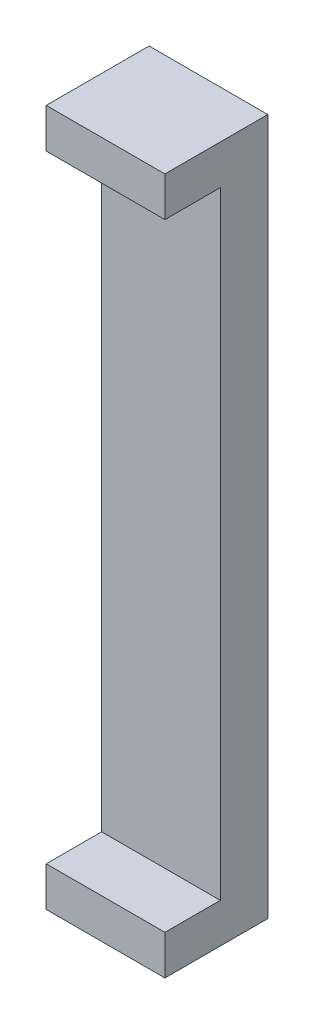
SolidWorks part; units mm, degrees
ref_plane "Front Plane" through (0, 0, 0) normal (0, 0, 1) x (1, 0, 0)
ref_plane "Top Plane" through (0, 0, 0) normal (0, 1, 0) x (1, 0, 0)
ref_plane "Right Plane" through (0, 0, 0) normal (1, 0, 0) x (0, 0, -1)
sketch "Sketch1" plane through (0, 0, 0) normal (0, 0, 1) x (1, 0, 0)
  line L1 (-7.5, 0) -> (7.5, 0)
  line L2 (-7.5, 0) -> (-7.5, 88)
  line L3 (-7.5, 88) -> (7.5, 88)
  line L4 (7.5, 0) -> (7.5, 88)
  point P4 (0, 0)
  dimension "D1" = 15
  dimension "D2" = 88
extrude "Boss-Extrude1" add sketch "Sketch1" along normal mid plane 6
sketch "Sketch2" plane through (0, 0, 0) normal (0, 0, 1) x (1, 0, 0)
  line L0 (7.5, 0) -> (7.5, 88) construction
  line L1 (-7.5, 0) -> (7.5, 0)
  line L2 (-7.5, 0) -> (-7.5, 5)
  line L3 (-7.5, 5) -> (7.5, 5)
  line L4 (7.5, 0) -> (7.5, 5)
  dimension "D1" = 5
extrude "Boss-Extrude2" add sketch "Sketch2" along normal blind 10
sketch "Sketch3" plane through (0, 0, 0) normal (0, 0, 1) x (1, 0, 0)
  line L0 (7.5, 5) -> (7.5, 88) construction
  line L1 (-7.5, 88) -> (7.5, 88)
  line L2 (-7.5, 88) -> (-7.5, 83)
  line L3 (-7.5, 83) -> (7.5, 83)
  line L4 (7.5, 88) -> (7.5, 83)
  dimension "D1" = 5
extrude "Boss-Extrude3" add sketch "Sketch3" along normal blind 10
